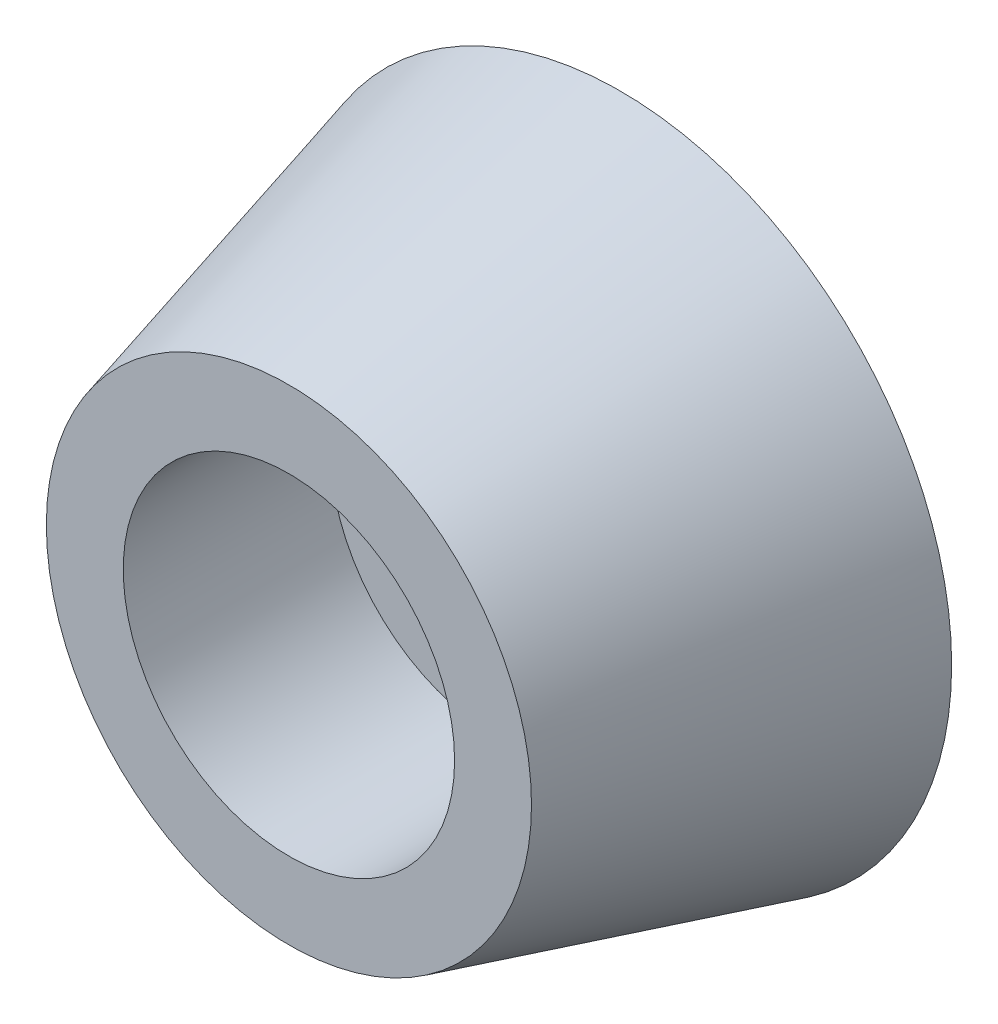
SolidWorks part; units mm, degrees
material "POLYURETHANE (11671)"
ref_plane "Front Plane" through (0, 0, 0) normal (0, 0, 1) x (1, 0, 0)
ref_plane "Top Plane" through (0, 0, 0) normal (0, 1, 0) x (1, 0, 0)
ref_plane "Right Plane" through (0, 0, 0) normal (1, 0, 0) x (0, 0, -1)
sketch "Sketch1" plane through (0, 0, 0) normal (0, 0, 1) x (1, 0, 0)
  circle A0 centre (0, 0) radius 6.35
  dimension "D1" = 12.7
extrude "Boss-Extrude1" add sketch "Sketch1" along normal blind 6.35 draft 15
sketch "Sketch2" plane through (0, 0, 6.35) normal (0, 0, 1) x (1, 0, 0)
  circle A0 centre (0, 0) radius 3.175
  dimension "D1" = 6.35
extrude "Cut-Extrude1" cut sketch "Sketch2" against normal blind 3.9688
sketch "Sketch3" plane through (0, 0, 2.3812) normal (0, 0, 1) x (1, 0, 0)
  circle A0 centre (0, 0) radius 1.5875
  dimension "D1" = 3.175
extrude "Cut-Extrude2" cut sketch "Sketch3" against normal through all
